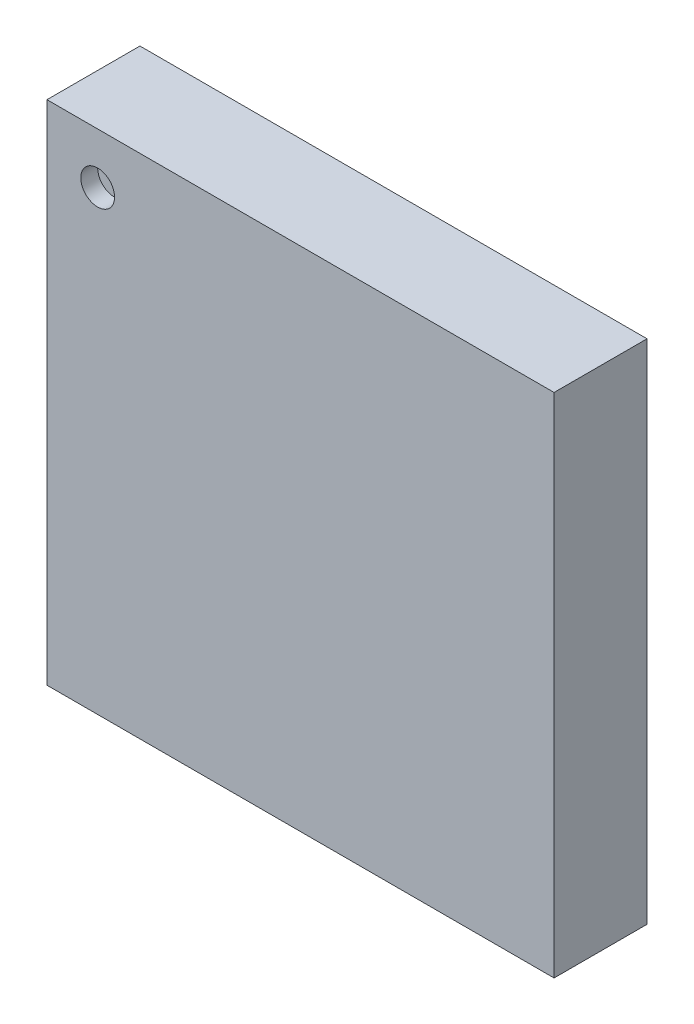
SolidWorks part; units mm, degrees
ref_plane "Front Plane" through (0, 0, 0) normal (0, 0, 1) x (1, 0, 0)
ref_plane "Top Plane" through (0, 0, 0) normal (0, 1, 0) x (1, 0, 0)
ref_plane "Right Plane" through (0, 0, 0) normal (1, 0, 0) x (0, 0, -1)
sketch "Sketch1" plane through (0, 0, 0) normal (0, 0, 1) x (1, 0, 0)
  line L1 (0, 0) -> (3, 0)
  line L2 (0, 0) -> (0, 3)
  line L3 (0, 3) -> (3, 3)
  line L4 (3, 0) -> (3, 3)
  dimension "D1" = 3
  dimension "D2" = 3
extrude "Boss-Extrude1" add sketch "Sketch1" along normal blind 0.55
sketch "Sketch2" plane through (0, 0, 0.55) normal (0, 0, 1) x (1, 0, 0)
  line L0 (0, 3) -> (0, 0) construction
  line L1 (3, 3) -> (0, 3) construction
  circle A0 centre (0.3, 2.7) radius 0.1
  dimension "D3" = 0.2
  dimension "D1" = 0.3
  dimension "D2" = 0.3
extrude "Cut-Extrude1" cut sketch "Sketch2" against normal blind 0.1
sketch "Sketch3" plane through (0, 0, 0) normal (0, 0, -1) x (-1, 0, 0)
  line L0 (-1.5, 3) -> (-1.5, 0) construction
  line L1 (-3, 3) -> (0, 3) construction
  line L2 (0, 0) -> (-3, 0) construction
  line L3 (-2.765, 2.925) -> (-2.765, 0.075) construction
  line L4 (-3, 0) -> (-3, 3) construction
  line L5 (-3, 1.5) -> (0, 1.5) construction
  line L6 (0, 3) -> (0, 0) construction
  line L7 (-2.925, 2.925) -> (-2.605, 2.925)
  line L8 (-2.925, 2.925) -> (-2.925, 2.605)
  line L9 (-2.925, 2.605) -> (-2.605, 2.605)
  line L10 (-2.605, 2.925) -> (-2.605, 2.605)
  line L11 (-0.395, 2.925) -> (-0.075, 2.925)
  line L12 (-2.925, 2.765) -> (-0.075, 2.765) construction
  line L13 (-0.395, 2.925) -> (-0.395, 2.605)
  line L14 (-0.395, 2.605) -> (-0.075, 2.605)
  line L15 (-0.075, 2.925) -> (-0.075, 2.605)
  line L16 (-0.395, 0.395) -> (-0.075, 0.395)
  line L17 (-0.395, 0.395) -> (-0.395, 0.075)
  line L18 (-0.395, 0.075) -> (-0.075, 0.075)
  line L19 (-0.075, 0.395) -> (-0.075, 0.075)
  line L20 (-2.925, 0.395) -> (-2.605, 0.395)
  line L21 (-2.925, 0.395) -> (-2.925, 0.075)
  line L22 (-2.925, 0.075) -> (-2.605, 0.075)
  line L23 (-2.605, 0.395) -> (-2.605, 0.075)
  line L24 (-0.85, 2.35) -> (-0.65, 2.15)
  line L25 (-2.35, 2.35) -> (-0.85, 2.35)
  line L26 (-2.35, 2.35) -> (-2.35, 0.65)
  line L27 (-2.35, 0.65) -> (-0.65, 0.65)
  line L28 (-0.65, 2.15) -> (-0.65, 0.65)
  line L29 (-0.235, 2.925) -> (-0.235, 0.075) construction
  line L30 (-2.25, 2.9) -> (-2.25, 2.5) construction
  line L31 (-2.925, 0.235) -> (-0.075, 0.235) construction
  line L32 (-2.375, 2.9) -> (-2.125, 2.9)
  line L33 (-2.375, 2.9) -> (-2.375, 2.6176)
  line L34 (-1.875, 2.9) -> (-1.625, 2.9)
  line L35 (-2.125, 2.9) -> (-2.125, 2.6176)
  line L36 (-1.875, 2.9) -> (-1.875, 2.6176)
  line L37 (-1.625, 2.9) -> (-1.625, 2.6176)
  line L38 (-1.75, 2.9) -> (-1.75, 2.5) construction
  line L39 (-1.375, 2.9) -> (-1.125, 2.9)
  line L40 (-1.375, 2.9) -> (-1.375, 2.6176)
  line L41 (-1.125, 2.9) -> (-1.125, 2.6176)
  line L42 (-1.25, 2.9) -> (-1.25, 2.5) construction
  line L43 (-0.875, 2.9) -> (-0.625, 2.9)
  line L44 (-0.875, 2.9) -> (-0.875, 2.6176)
  line L45 (-0.625, 2.9) -> (-0.625, 2.6176)
  line L46 (-0.75, 2.9) -> (-0.75, 2.5) construction
  line L47 (-0.1, 2.375) -> (-0.1, 2.125)
  line L48 (-0.1, 2.375) -> (-0.3824, 2.375)
  line L49 (-0.1, 1.875) -> (-0.1, 1.625)
  line L50 (-0.1, 2.125) -> (-0.3824, 2.125)
  line L51 (-0.1, 1.875) -> (-0.3824, 1.875)
  line L52 (-0.1, 1.625) -> (-0.3824, 1.625)
  line L53 (-0.1, 1.375) -> (-0.1, 1.125)
  line L54 (-0.1, 1.375) -> (-0.3824, 1.375)
  line L55 (-0.1, 1.125) -> (-0.3824, 1.125)
  line L56 (-0.1, 0.875) -> (-0.1, 0.625)
  line L57 (-0.1, 0.875) -> (-0.3824, 0.875)
  line L58 (-0.1, 0.625) -> (-0.3824, 0.625)
  line L59 (-0.1, 2.25) -> (-0.5, 2.25) construction
  line L60 (-0.1, 1.75) -> (-0.5, 1.75) construction
  line L61 (-0.1, 1.25) -> (-0.5, 1.25) construction
  line L62 (-0.1, 0.75) -> (-0.5, 0.75) construction
  line L63 (-0.625, 0.1) -> (-0.875, 0.1)
  line L64 (-0.625, 0.1) -> (-0.625, 0.3824)
  line L65 (-1.125, 0.1) -> (-1.375, 0.1)
  line L66 (-0.875, 0.1) -> (-0.875, 0.3824)
  line L67 (-1.125, 0.1) -> (-1.125, 0.3824)
  line L68 (-1.375, 0.1) -> (-1.375, 0.3824)
  line L69 (-1.625, 0.1) -> (-1.875, 0.1)
  line L70 (-1.625, 0.1) -> (-1.625, 0.3824)
  line L71 (-1.875, 0.1) -> (-1.875, 0.3824)
  line L72 (-2.125, 0.1) -> (-2.375, 0.1)
  line L73 (-2.125, 0.1) -> (-2.125, 0.3824)
  line L74 (-2.375, 0.1) -> (-2.375, 0.3824)
  line L75 (-0.75, 0.1) -> (-0.75, 0.5) construction
  line L76 (-1.25, 0.1) -> (-1.25, 0.5) construction
  line L77 (-1.75, 0.1) -> (-1.75, 0.5) construction
  line L78 (-2.25, 0.1) -> (-2.25, 0.5) construction
  line L79 (-2.9, 0.625) -> (-2.9, 0.875)
  line L80 (-2.9, 0.625) -> (-2.6176, 0.625)
  line L81 (-2.9, 1.125) -> (-2.9, 1.375)
  line L82 (-2.9, 0.875) -> (-2.6176, 0.875)
  line L83 (-2.9, 1.125) -> (-2.6176, 1.125)
  line L84 (-2.9, 1.375) -> (-2.6176, 1.375)
  line L85 (-2.9, 1.625) -> (-2.9, 1.875)
  line L86 (-2.9, 1.625) -> (-2.6176, 1.625)
  line L87 (-2.9, 1.875) -> (-2.6176, 1.875)
  line L88 (-2.9, 2.125) -> (-2.9, 2.375)
  line L89 (-2.9, 2.125) -> (-2.6176, 2.125)
  line L90 (-2.9, 2.375) -> (-2.6176, 2.375)
  line L91 (-2.9, 0.75) -> (-2.5, 0.75) construction
  line L92 (-2.9, 1.25) -> (-2.5, 1.25) construction
  line L93 (-2.9, 1.75) -> (-2.5, 1.75) construction
  line L94 (-2.9, 2.25) -> (-2.5, 2.25) construction
  arc A0 (-2.375, 2.6176) -> (-2.125, 2.6176) centre (-2.25, 2.6252) ccw
  arc A1 (-1.875, 2.6176) -> (-1.625, 2.6176) centre (-1.75, 2.6252) ccw
  arc A2 (-1.375, 2.6176) -> (-1.125, 2.6176) centre (-1.25, 2.6252) ccw
  arc A3 (-0.875, 2.6176) -> (-0.625, 2.6176) centre (-0.75, 2.6252) ccw
  arc A4 (-0.3824, 2.375) -> (-0.3824, 2.125) centre (-0.3748, 2.25) ccw
  arc A5 (-0.3824, 1.875) -> (-0.3824, 1.625) centre (-0.3748, 1.75) ccw
  arc A6 (-0.3824, 1.375) -> (-0.3824, 1.125) centre (-0.3748, 1.25) ccw
  arc A7 (-0.3824, 0.875) -> (-0.3824, 0.625) centre (-0.3748, 0.75) ccw
  arc A8 (-0.625, 0.3824) -> (-0.875, 0.3824) centre (-0.75, 0.3748) ccw
  arc A9 (-1.125, 0.3824) -> (-1.375, 0.3824) centre (-1.25, 0.3748) ccw
  arc A10 (-1.625, 0.3824) -> (-1.875, 0.3824) centre (-1.75, 0.3748) ccw
  arc A11 (-2.125, 0.3824) -> (-2.375, 0.3824) centre (-2.25, 0.3748) ccw
  arc A12 (-2.6176, 0.625) -> (-2.6176, 0.875) centre (-2.6252, 0.75) ccw
  arc A13 (-2.6176, 1.125) -> (-2.6176, 1.375) centre (-2.6252, 1.25) ccw
  arc A14 (-2.6176, 1.625) -> (-2.6176, 1.875) centre (-2.6252, 1.75) ccw
  arc A15 (-2.6176, 2.125) -> (-2.6176, 2.375) centre (-2.6252, 2.25) ccw
  point P36 (-1.5, 0.65)
  point P37 (-2.35, 1.5)
  point P44 (-1.5, 1.5)
  point P159 (-1.5, 1.5)
  dimension "D11" = 0.4
  dimension "D1" = 0.32
  dimension "D2" = 0.32
  dimension "D3" = 1.265
  dimension "D4" = 1.265
  dimension "D7" = 1.7
  dimension "D8" = 135
  dimension "D9" = 1.5
  dimension "D10" = 0.25
  dimension "D12" = 0.1
  dimension "D13" = 0.75
  dimension "D14" = 0.2824
  dimension "D5" = 2
  dimension "D6" = 2
  dimension "D15" = 4
  dimension "D16" = 4
extrude "Boss-Extrude2" add sketch "Sketch3" along normal blind 0.02
